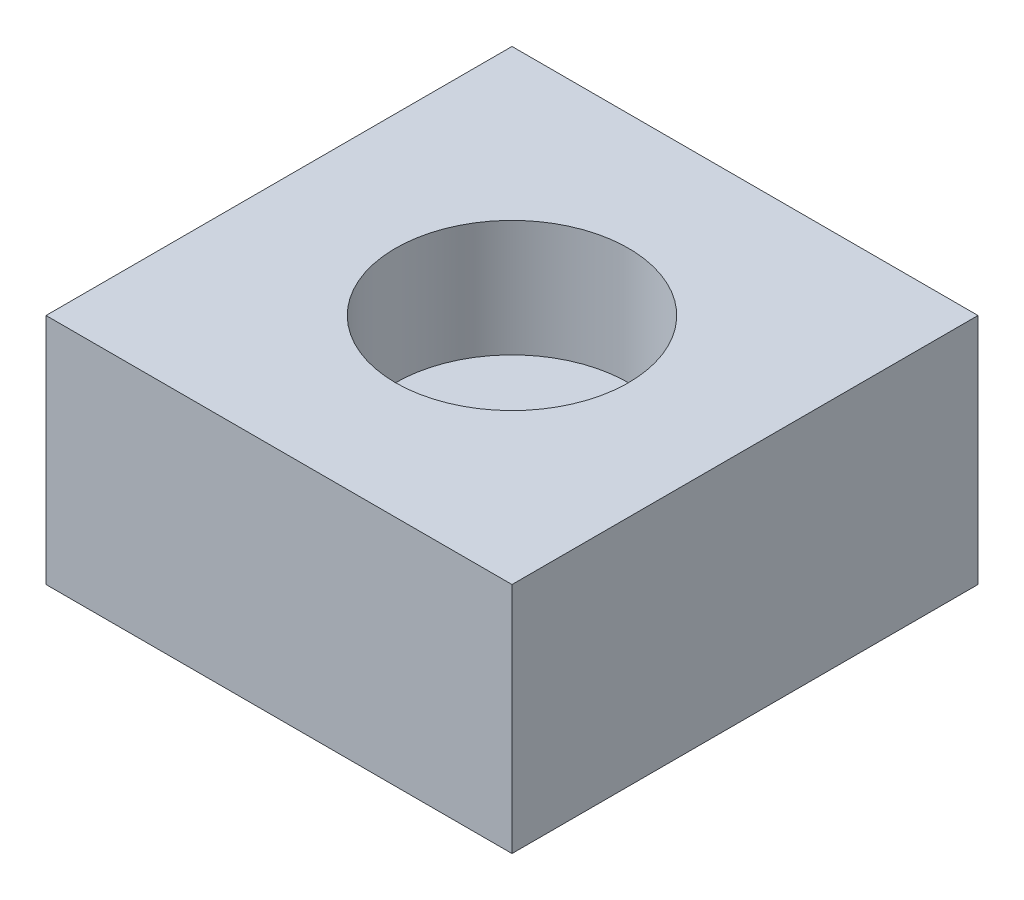
SolidWorks part; units mm, degrees
ref_plane "Front Plane" through (0, 0, 0) normal (0, 0, 1) x (1, 0, 0)
ref_plane "Top Plane" through (0, 0, 0) normal (0, 1, 0) x (1, 0, 0)
ref_plane "Right Plane" through (0, 0, 0) normal (1, 0, 0) x (0, 0, -1)
sketch "Sketch1" plane through (0, 0, 0) normal (0, 1, 0) x (1, 0, 0)
  line L1 (0, 0) -> (20, 0)
  line L2 (0, 0) -> (0, 20)
  line L3 (0, 20) -> (20, 20)
  line L4 (20, 0) -> (20, 20)
  dimension "D1" = 20
  dimension "D2" = 20
extrude "Boss-Extrude1" add sketch "Sketch1" along normal blind 10
sketch "Sketch2" plane through (0, 10, 0) normal (0, 1, 0) x (-1, 0, 0)
  line L0 (-10, -10) -> (-10, 0) construction
  line L1 (0, 0) -> (-20, 0) construction
  line L2 (-10, -10) -> (0, -10) construction
  line L3 (0, -20) -> (0, 0) construction
  circle A0 centre (-10, -10) radius 5
  dimension "D1" = 10
extrude "Cut-Extrude1" cut sketch "Sketch2" against normal blind 5
